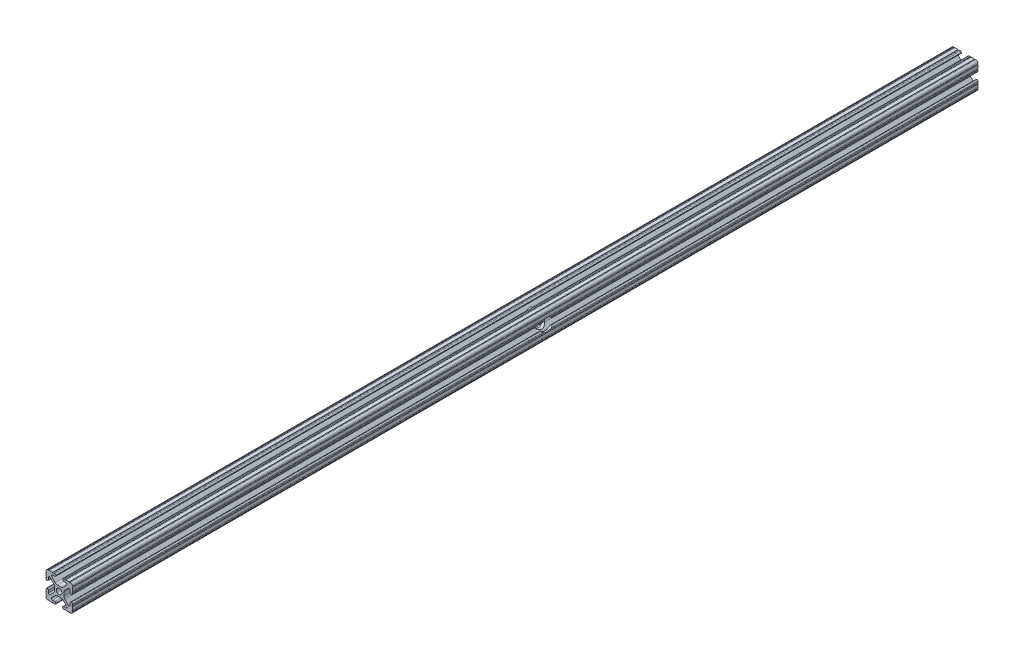
SolidWorks part; units mm, degrees
material "6063-T5"
ref_plane "Front Plane" through (0, 0, 0) normal (0, 0, 1) x (1, 0, 0)
ref_plane "Top Plane" through (0, 0, 0) normal (0, 1, 0) x (1, 0, 0)
ref_plane "Right Plane" through (0, 0, 0) normal (1, 0, 0) x (0, 0, -1)
sketch "Sketch1" plane through (0, 0, 0) normal (0, 0, 1) x (1, 0, 0)
  line L0 (-7.207, 8.7244) -> (-3.8983, 5.4232)
  line L1 (-4.2875, 10.4902) -> (-6.4768, 10.4902)
  line L2 (-3.2385, 11.651) -> (-3.2385, 11.5392)
  line L3 (-5.3171, 12.7) -> (-4.2875, 12.7)
  line L4 (0, 13.4005) -> (0, -14.8534) construction
  line L5 (12.7, 0) -> (-13.9989, 0) construction
  line L6 (-9.5504, 12.7) -> (-6.3331, 12.7)
  line L7 (-12.7, 6.3331) -> (-12.7, 9.5504)
  line L8 (-12.7, 4.2875) -> (-12.7, 5.3171)
  line L9 (-11.5392, 3.2385) -> (-11.651, 3.2385)
  line L10 (-10.4902, 6.4021) -> (-10.4902, 4.2875)
  line L11 (-5.441, 3.8408) -> (-8.7371, 7.1294)
  line L12 (-4.5085, -1.5932) -> (-4.5085, 1.5932)
  line L13 (-1.7093, -4.4958) -> (1.7093, -4.4958)
  line L14 (3.9523, -5.4237) -> (7.1797, -8.6452)
  line L15 (6.4164, -10.4902) -> (4.2875, -10.4902)
  line L16 (3.2385, -11.5392) -> (3.2385, -11.651)
  line L17 (4.2875, -12.7) -> (5.3171, -12.7)
  line L18 (6.3331, -12.7) -> (9.5504, -12.7)
  line L19 (12.7, -9.5504) -> (12.7, -6.3331)
  line L20 (12.7, -5.3171) -> (12.7, -4.2875)
  line L21 (11.651, -3.2385) -> (11.5392, -3.2385)
  line L22 (10.4902, -4.2875) -> (10.4902, -6.4021)
  line L23 (8.7371, -7.1294) -> (5.441, -3.8408)
  line L24 (4.5085, -1.5932) -> (4.5085, 1.5932)
  line L25 (5.441, 3.8408) -> (8.7371, 7.1294)
  line L26 (10.4902, 6.4021) -> (10.4902, 4.2875)
  line L27 (11.5392, 3.2385) -> (11.651, 3.2385)
  line L28 (12.7, 4.2875) -> (12.7, 5.3171)
  line L29 (12.7, 6.3331) -> (12.7, 9.5504)
  line L30 (9.5504, 12.7) -> (6.3331, 12.7)
  line L31 (5.3171, 12.7) -> (4.2875, 12.7)
  line L32 (3.2385, 11.651) -> (3.2385, 11.5392)
  line L33 (4.2875, 10.4902) -> (6.4768, 10.4902)
  line L34 (7.207, 8.7244) -> (3.8983, 5.4232)
  line L35 (1.6558, 4.4958) -> (-1.6558, 4.4958)
  line L36 (-8.7371, -7.1294) -> (-5.441, -3.8408)
  line L37 (-10.4902, -4.2875) -> (-10.4902, -6.4021)
  line L38 (-11.651, -3.2385) -> (-11.5392, -3.2385)
  line L39 (-12.7, -5.3171) -> (-12.7, -4.2875)
  line L40 (-12.7, -9.5504) -> (-12.7, -6.3331)
  line L41 (-6.3331, -12.7) -> (-9.5504, -12.7)
  line L42 (-4.2875, -12.7) -> (-5.3171, -12.7)
  line L43 (-3.2385, -11.5392) -> (-3.2385, -11.651)
  line L44 (-6.4164, -10.4902) -> (-4.2875, -10.4902)
  line L45 (-3.9523, -5.4237) -> (-7.1797, -8.6452)
  arc A0 (-7.207, 8.7244) -> (-6.4768, 10.4902) centre (-6.4768, 9.4563) cw
  arc A1 (-3.2385, 11.5392) -> (-4.2875, 10.4902) centre (-4.2875, 11.5392) cw
  arc A2 (-4.2875, 12.7) -> (-3.2385, 11.651) centre (-4.2875, 11.651) cw
  arc A3 (-5.3171, 12.7) -> (-6.3331, 12.7) centre (-5.8251, 12.7) cw
  arc A4 (-9.5504, 12.7) -> (-10.5664, 12.6998) centre (-10.0584, 12.7) cw
  arc A5 (-12.6998, 10.5664) -> (-10.5664, 12.6998) centre (-10.5918, 10.5918) cw
  arc A6 (-12.6998, 10.5664) -> (-12.7, 9.5504) centre (-12.7, 10.0584) cw
  arc A7 (-12.7, 6.3331) -> (-12.7, 5.3171) centre (-12.7, 5.8251) cw
  arc A8 (-11.651, 3.2385) -> (-12.7, 4.2875) centre (-11.651, 4.2875) cw
  arc A9 (-10.4902, 4.2875) -> (-11.5392, 3.2385) centre (-11.5392, 4.2875) cw
  circle A10 centre (0, 0) radius 2.6035
  arc A11 (-10.4902, 6.4021) -> (-8.7371, 7.1294) centre (-9.4628, 6.4021) cw
  arc A12 (-5.441, 3.8408) -> (-4.5085, 1.5932) centre (-7.6835, 1.5932) cw
  arc A13 (-4.5085, -1.5932) -> (-5.441, -3.8408) centre (-7.6835, -1.5932) cw
  arc A14 (-8.7371, -7.1294) -> (-10.4902, -6.4021) centre (-9.4628, -6.4021) cw
  arc A15 (-1.7093, -4.4958) -> (-3.9523, -5.4237) centre (-1.7093, -7.6708) ccw
  arc A16 (3.9523, -5.4237) -> (1.7093, -4.4958) centre (1.7093, -7.6708) ccw
  arc A17 (6.4164, -10.4902) -> (7.1797, -8.6452) centre (6.4164, -9.4098) ccw
  arc A18 (4.2875, -10.4902) -> (3.2385, -11.5392) centre (4.2875, -11.5392) ccw
  arc A19 (3.2385, -11.651) -> (4.2875, -12.7) centre (4.2875, -11.651) ccw
  arc A20 (6.3331, -12.7) -> (5.3171, -12.7) centre (5.8251, -12.7) ccw
  arc A21 (10.5664, -12.6998) -> (9.5504, -12.7) centre (10.0584, -12.7) ccw
  arc A22 (10.5664, -12.6998) -> (12.6998, -10.5664) centre (10.5918, -10.5918) ccw
  arc A23 (12.7, -9.5504) -> (12.6998, -10.5664) centre (12.7, -10.0584) ccw
  arc A24 (12.7, -5.3171) -> (12.7, -6.3331) centre (12.7, -5.8251) ccw
  arc A25 (12.7, -4.2875) -> (11.651, -3.2385) centre (11.651, -4.2875) ccw
  arc A26 (11.5392, -3.2385) -> (10.4902, -4.2875) centre (11.5392, -4.2875) ccw
  arc A27 (8.7371, -7.1294) -> (10.4902, -6.4021) centre (9.4628, -6.4021) ccw
  arc A28 (4.5085, -1.5932) -> (5.441, -3.8408) centre (7.6835, -1.5932) ccw
  arc A29 (5.441, 3.8408) -> (4.5085, 1.5932) centre (7.6835, 1.5932) ccw
  arc A30 (10.4902, 6.4021) -> (8.7371, 7.1294) centre (9.4628, 6.4021) ccw
  arc A31 (10.4902, 4.2875) -> (11.5392, 3.2385) centre (11.5392, 4.2875) ccw
  arc A32 (11.651, 3.2385) -> (12.7, 4.2875) centre (11.651, 4.2875) ccw
  arc A33 (12.7, 6.3331) -> (12.7, 5.3171) centre (12.7, 5.8251) ccw
  arc A34 (12.6998, 10.5664) -> (12.7, 9.5504) centre (12.7, 10.0584) ccw
  arc A35 (12.6998, 10.5664) -> (10.5664, 12.6998) centre (10.5918, 10.5918) ccw
  arc A36 (9.5504, 12.7) -> (10.5664, 12.6998) centre (10.0584, 12.7) ccw
  arc A37 (5.3171, 12.7) -> (6.3331, 12.7) centre (5.8251, 12.7) ccw
  arc A38 (4.2875, 12.7) -> (3.2385, 11.651) centre (4.2875, 11.651) ccw
  arc A39 (3.2385, 11.5392) -> (4.2875, 10.4902) centre (4.2875, 11.5392) ccw
  arc A40 (7.207, 8.7244) -> (6.4768, 10.4902) centre (6.4768, 9.4563) ccw
  arc A41 (1.6558, 4.4958) -> (3.8983, 5.4232) centre (1.6558, 7.6708) ccw
  arc A42 (-1.6558, 4.4958) -> (-3.8983, 5.4232) centre (-1.6558, 7.6708) cw
  arc A43 (-11.5392, -3.2385) -> (-10.4902, -4.2875) centre (-11.5392, -4.2875) cw
  arc A44 (-12.7, -4.2875) -> (-11.651, -3.2385) centre (-11.651, -4.2875) cw
  arc A45 (-12.7, -5.3171) -> (-12.7, -6.3331) centre (-12.7, -5.8251) cw
  arc A46 (-12.7, -9.5504) -> (-12.6998, -10.5664) centre (-12.7, -10.0584) cw
  arc A47 (-10.5664, -12.6998) -> (-12.6998, -10.5664) centre (-10.5918, -10.5918) cw
  arc A48 (-10.5664, -12.6998) -> (-9.5504, -12.7) centre (-10.0584, -12.7) cw
  arc A49 (-6.3331, -12.7) -> (-5.3171, -12.7) centre (-5.8251, -12.7) cw
  arc A50 (-3.2385, -11.651) -> (-4.2875, -12.7) centre (-4.2875, -11.651) cw
  arc A51 (-4.2875, -10.4902) -> (-3.2385, -11.5392) centre (-4.2875, -11.5392) cw
  arc A52 (-6.4164, -10.4902) -> (-7.1797, -8.6452) centre (-6.4164, -9.4098) cw
  dimension "D1" = 5.207
  dimension "D9" = 14.859
  dimension "D2" = 25.4
  dimension "D3" = 12.7
  dimension "D4" = 6.477
  dimension "D5" = 8.2042
  dimension "D6" = 9.017
  dimension "D8" = 2.2098
  dimension "D10" = 2.2098
extrude "Extrude1" add sketch "Sketch1" against normal blind 1219.2
sketch "Sketch2" plane through (0, 12.7, 0) normal (0, 1, 0) x (1, 0, 0)
  line L0 (20.849, 870) -> (-9.5504, 870) construction
  line L2 (-9.5504, 1219.2) -> (-9.5504, 0) construction
  line L4 (20.849, 870) -> (-46.7134, 870)
  line L5 (20.849, 870) -> (20.849, 1239.9082)
  line L6 (20.849, 1239.9082) -> (-46.7134, 1239.9082)
  line L7 (-46.7134, 870) -> (-46.7134, 1239.9082)
  dimension "D1" = 870
extrude "Cut-Extrude2" cut sketch "Sketch2" against normal through all
sketch "Sketch3" plane through (4.5085, 0, 0) normal (1, 0, 0) x (0, 0, -1)
  line L0 (0, 0) -> (450.1, 0) construction
  line L1 (0, -1.5932) -> (0, 1.5932) construction
  line L2 (462.1, 1.5932) -> (462.1, -1.5932) construction
  line L3 (870, 1.5932) -> (0, 1.5932) construction
  line L4 (870, -1.5932) -> (0, -1.5932) construction
  circle A0 centre (456.1, 0) radius 6
  point P12 (462.1, 0)
  point P13 (462.1, 0)
  dimension "D2" = 12
  dimension "D1" = 450.1
extrude "Cut-Extrude3" cut sketch "Sketch3" against normal through all both and the other way through all
